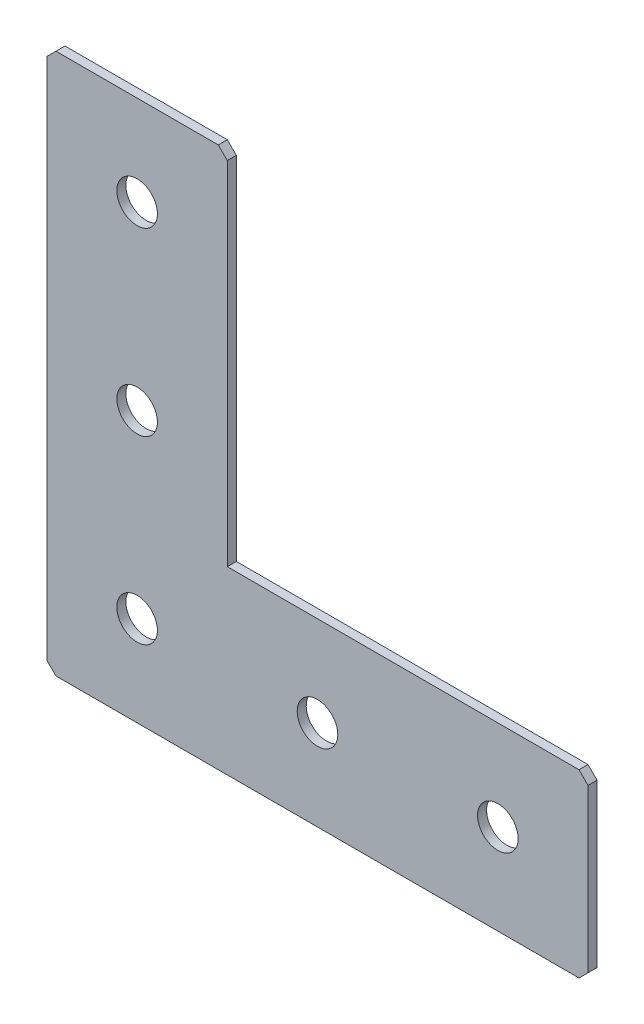
SolidWorks part; units mm, degrees
material "Простая углеродистая сталь"
ref_plane "Спереди(Плоскость XY)" through (0, 0, 0) normal (0, 0, 1) x (1, 0, 0)
ref_plane "Сверху(Плоскость XZ)" through (0, 0, 0) normal (0, 1, 0) x (1, 0, 0)
ref_plane "Справа(Плоскость ZY)" through (0, 0, 0) normal (1, 0, 0) x (0, 0, -1)
sketch "Эскиз1" plane through (0, 0, 0) normal (0, 0, -1) x (1, 0, 0)
  line L0 (0, 0) -> (0, 120)
  line L1 (0, 120) -> (120, 120)
  line L2 (120, 120) -> (120, 80)
  line L3 (120, 80) -> (40, 80)
  line L4 (40, 80) -> (40, 0)
  line L5 (40, 0) -> (0, 0)
  dimension "D1" = 120
  dimension "D3" = 40
extrude "Бобышка-Вытянуть1" add sketch "Эскиз1" along normal blind 2
hole_wizard "Отверстие с зазором M81" positions "Эскиз2" profile "Эскиз3" hole size "M8" standard "DIN" end condition through all
sketch "Эскиз2" plane through (0, 0, -2) normal (0, 0, -1) x (1, 0, 0)
  line L0 (20, 0) -> (20, 100) construction
  line L1 (0, 0) -> (40, 0) construction
  line L3 (120, 100) -> (0, 100) construction
  line L5 (0, 120) -> (0, 0) construction
  line L6 (120, 80) -> (120, 120) construction
  point P0 (60, 100)
  point P2 (20, 100)
  point P4 (20, 60)
  point P6 (20, 20)
  point P21 (100, 100)
  dimension "D1" = 40
  dimension "D2" = 40
  dimension "D3" = 40
  dimension "D4" = 20
  dimension "D5" = 40
sketch "Эскиз3" plane through (60, -100, -2) normal (1, 0, 0) x (0, 1, 0)
  line L0 (0, 0) -> (0, 2)
  line L1 (0, 2) -> (4.5, 2)
  line L2 (4.5, 2) -> (4.5, 0)
  line L5 (4.5, 0) -> (0, 0)
  line L11 (0, -6.35) -> (0, 107.95) construction
  dimension "Диаметр сквозного отверстия" = 9
  dimension "Глубина сквозного отверстия" = 2
chamfer "Фаска1" distance 2 angle 45 5 edges at (0, 0, -1) (40, 0, -1) (120, -80, -1) (120, -120, -1) (0, -120, -1)
